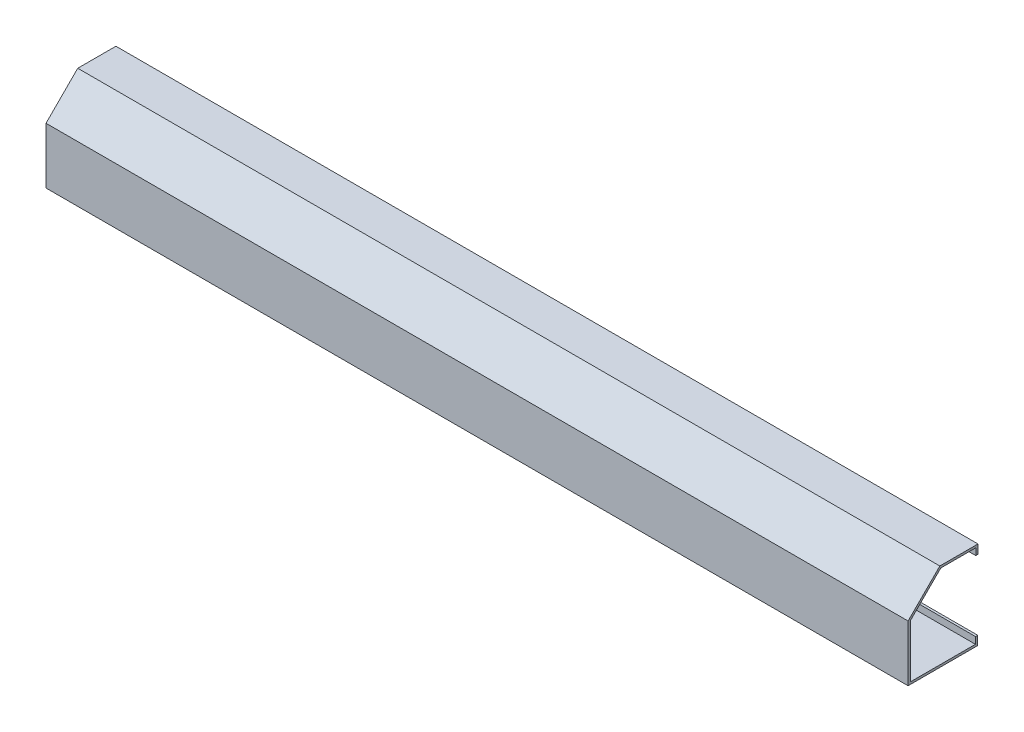
SolidWorks part; units mm, degrees
ref_plane "Alzado" through (0, 0, 0) normal (0, 0, 1) x (1, 0, 0)
ref_plane "Planta" through (0, 0, 0) normal (0, 1, 0) x (1, 0, 0)
ref_plane "Vista lateral" through (0, 0, 0) normal (1, 0, 0) x (0, 0, -1)
sketch "Croquis1" plane through (0, 0, 0) normal (1, 0, 0) x (0, 0, -1)
  line L0 (0, 0) -> (196.85, 0)
  line L1 (196.85, 0) -> (196.85, 25.4)
  line L5 (6.35, 6.35) -> (6.35, 156.1197)
  line L6 (6.35, 156.1197) -> (92.4328, 242.2026)
  line L7 (92.4328, 242.2026) -> (191.4026, 242.2026)
  line L8 (191.4026, 242.2026) -> (191.4026, 223.1526)
  line L9 (191.4026, 223.1526) -> (197.7526, 223.1526)
  line L10 (197.7526, 223.1526) -> (197.7526, 248.5526)
  line L11 (197.7526, 248.5526) -> (89.8026, 248.5526)
  line L12 (89.8026, 248.5526) -> (0, 158.75)
  line L13 (0, 158.75) -> (0, 0)
  line L14 (196.85, 25.4) -> (190.5, 25.4)
  line L15 (190.5, 25.4) -> (190.5, 6.35)
  line L16 (190.5, 6.35) -> (6.35, 6.35)
  line L17 (6.35, 156.1197) -> (33.0086, 156.1197) construction
  point P5 (0, 0)
  dimension "D2" = 25.4
  dimension "D3" = 158.75
  dimension "D4" = 127
  dimension "D5" = 107.95
  dimension "D6" = 6.35
  dimension "D7" = 6.35
  dimension "D8" = 6.35
  dimension "D9" = 6.35
  dimension "D10" = 6.35
  dimension "D11" = 6.35
  dimension "D12" = 45
  dimension "D13" = 25.4
  dimension "D14" = 196.85
extrude "Saliente-Extruir1" add sketch "Croquis1" along normal blind 2438.4
